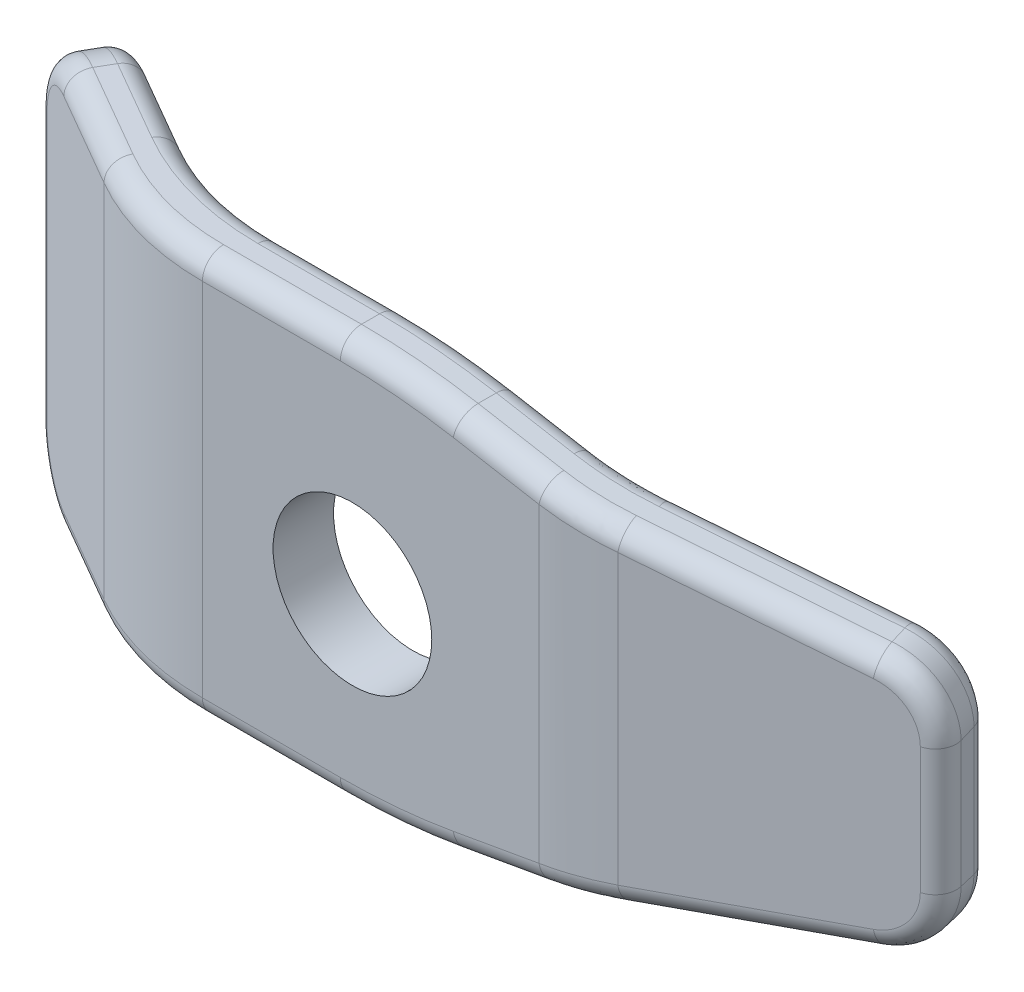
SolidWorks part; units mm, degrees
ref_plane "Front Plane" through (0, 0, 0) normal (0, 0, 1) x (1, 0, 0)
ref_plane "Top Plane" through (0, 0, 0) normal (0, 1, 0) x (1, 0, 0)
ref_plane "Right Plane" through (0, 0, 0) normal (1, 0, 0) x (0, 0, -1)
sketch "Sketch1" plane through (0, 0, 0) normal (0, 1, 0) x (1, 0, 0)
  line L0 (-69.3094, 21.997) -> (-31.2094, 0)
  line L1 (-31.2094, 0) -> (48.1656, 0)
  line L2 (48.1656, 0) -> (102.1406, 14.4626)
  line L3 (-75.0244, 12.0984) -> (-34.272, -11.43)
  line L4 (-34.272, -11.43) -> (49.6704, -11.43)
  line L5 (49.6704, -11.43) -> (105.0989, 3.422)
  line L6 (-69.3094, 21.997) -> (-75.0244, 12.0984)
  line L7 (105.0989, 3.422) -> (102.1406, 14.4626)
  dimension "D1" = 79.375
  dimension "D2" = 38.1
  dimension "D3" = 53.975
  dimension "D4" = 30
  dimension "D5" = 15
  dimension "D6" = 11.43
extrude "Boss-Extrude1" add sketch "Sketch1" along normal blind 76.2
sketch "Sketch2" plane through (0, 0, 11.43) normal (0, 0, 1) x (1, 0, 0)
  line L0 (16.528, 76.2) -> (105.0989, 60.5825)
  line L1 (-34.272, 76.2) -> (49.6704, 76.2) construction
  line L2 (-34.272, 76.2) -> (-34.272, 0) construction
  line L3 (105.0989, 76.2) -> (105.0989, 0) construction
  line L4 (105.0989, 76.2) -> (105.0989, 60.5825)
  line L5 (16.528, 76.2) -> (105.0989, 76.2)
  line L6 (105.0989, 38.1) -> (138.7211, 38.1) construction
  line L7 (16.528, 0) -> (105.0989, 15.6175)
  line L8 (105.0989, 0) -> (105.0989, 15.6175)
  line L9 (16.528, 0) -> (105.0989, 0)
  dimension "D1" = 50.8
  dimension "D2" = 10
extrude "Cut-Extrude1" cut sketch "Sketch2" against normal blind 76.2
sketch "Sketch3" plane through (0, 0, 11.43) normal (0, 0, 1) x (1, 0, 0)
  line L0 (49.6704, 70.3561) -> (-34.272, 0) construction
  line L1 (16.528, 76.2) -> (49.6704, 70.3561) construction
  line L2 (-75.0244, 0) -> (-34.272, 0) construction
  line L3 (-34.272, 0) -> (16.528, 0) construction
  circle A0 centre (7.6992, 35.178) radius 15
  point P17 (7.6992, 35.178)
  dimension "D1" = 30
extrude "Cut-Extrude2" cut sketch "Sketch3" against normal blind 50.8
fillet "Fillet1" radius 50.8 2 edges at (49.6704, 38.1, 11.43) (-34.272, 38.1, 11.43)
fillet "Fillet2" radius 50.8 2 edges at (48.1656, 38.1, 0) (-31.2094, 38.1, 0)
fillet "Fillet3" radius 127 2 edges at (16.528, 0, 5.715) (16.528, 76.2, 5.715)
fillet "Fillet4" radius 12.7 4 edges at (103.6198, 60.8434, -8.9423) (103.6198, 15.3566, -8.9423) (-72.1669, 76.2, -17.0477) (-72.1669, 0, -17.0477)
fillet "Fillet5" radius 4 40 edges at (-33.8082, 76.2, 9.699) (-55.043, 76.2, -0.5621) (-71.803, 72.4803, -10.2385) (-75.0244, 38.1, -12.0984) (-71.803, 3.7197, -10.2385) (-55.043, 0, -0.5621) (-33.8082, 0, 9.699) (-7.6216, 0, 11.43) (16.4857, 0.4833, 11.43) (35.2264, 3.297, 11.43) (49.6132, 5.8338, 10.9954) (75.5099, 10.4001, 4.5063) (102.2052, 18.1492, -2.6467) (105.0989, 38.1, -3.422) (102.2052, 58.0508, -2.6467) (75.5099, 65.7999, 4.5063) (49.6132, 70.3662, 10.9954) (35.2264, 72.903, 11.43) (16.4857, 75.7167, 11.43) (73.2783, 66.1934, -6.7289) (99.2469, 58.5724, -13.6872) (102.1406, 38.1, -14.4626) (99.2469, 17.6276, -13.6872) (73.2783, 10.0066, -6.7289) (48.1084, 5.5685, -0.4346) (34.474, 3.1644, 0) (16.4857, 0.4833, 0) (-6.0903, 0, 0) (-30.7456, 0, -1.731) (-50.6542, 0, -11.2265) (-66.088, 3.7197, -20.1372) (-69.3094, 38.1, -21.997) (-66.088, 72.4803, -20.1372) (-50.6542, 76.2, -11.2265) (-30.7456, 76.2, -1.731) (-6.0903, 76.2, 0) (16.4857, 75.7167, 0) (34.474, 73.0356, 0) (-7.6216, 76.2, 11.43) (48.1084, 70.6315, -0.4346)
scale "Scale1" scale about centroid uniform scaling yes scale factor 0.06
